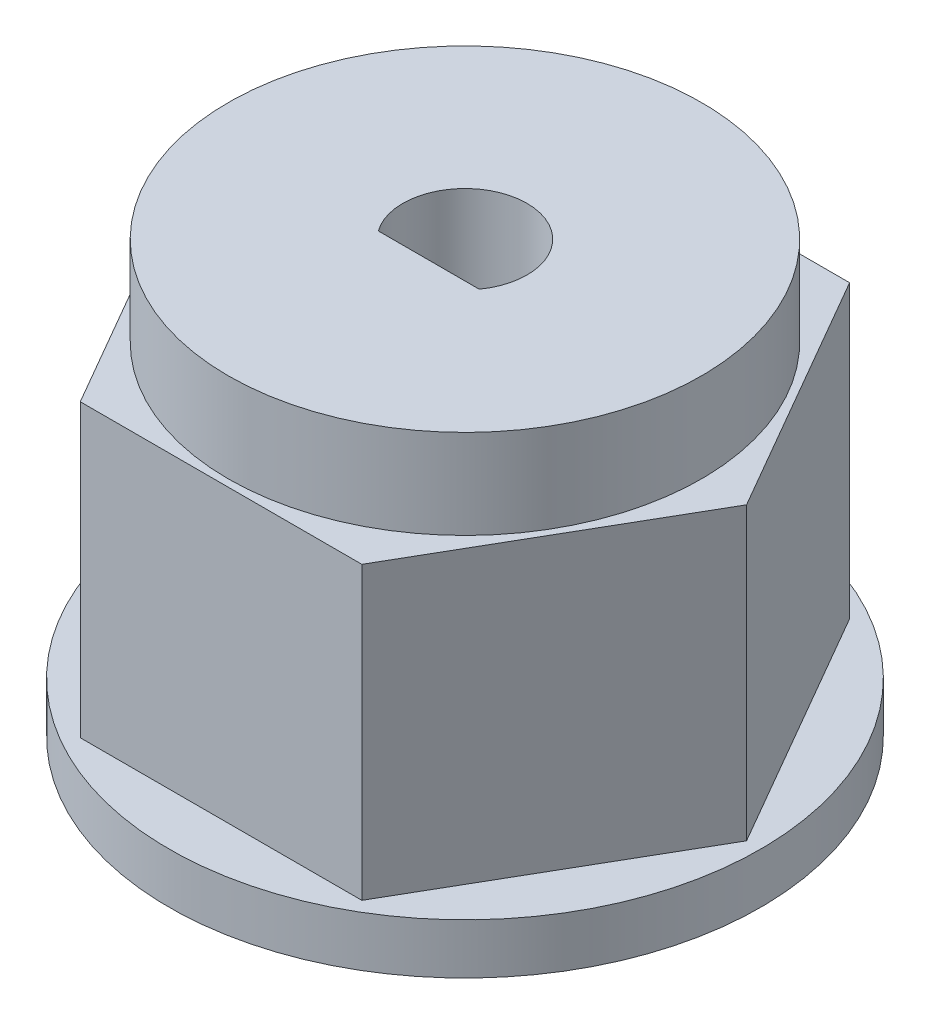
SolidWorks part; units mm, degrees
ref_plane "Front Plane" through (0, 0, 0) normal (0, 0, 1) x (1, 0, 0)
ref_plane "Top Plane" through (0, 0, 0) normal (0, 1, 0) x (1, 0, 0)
ref_plane "Right Plane" through (0, 0, 0) normal (1, 0, 0) x (0, 0, -1)
sketch "Sketch1" plane through (0, 0, 0) normal (0, 1, 0) x (1, 0, 0)
  line L1 (7.2573, 0) -> (3.6286, 6.285)
  line L2 (3.6286, 6.285) -> (-3.6286, 6.285)
  line L3 (-3.6286, 6.285) -> (-7.2573, 0)
  line L4 (-7.2573, 0) -> (-3.6286, -6.285)
  line L5 (-3.6286, -6.285) -> (3.6286, -6.285)
  line L6 (3.6286, -6.285) -> (7.2573, 0)
  circle A0 centre (0, 0) radius 6.285 construction
  dimension "D1" = 12.57
extrude "Boss-Extrude1" add sketch "Sketch1" along normal blind 7.5
sketch "Sketch2" plane through (0, 7.5, 0) normal (0, 1, 0) x (1, 0, 0)
  circle A0 centre (0, 0) radius 6.1
  dimension "D1" = 12.2
extrude "Boss-Extrude2" add sketch "Sketch2" along normal blind 2.3
sketch "Sketch3" plane through (0, 0, 0) normal (0, -1, 0) x (1, 0, 0)
  circle A0 centre (0, 0) radius 7.625
  dimension "D1" = 15.25
extrude "Boss-Extrude3" add sketch "Sketch3" along normal blind 1.3
sketch "Sketch4" plane through (0, 9.8, 0) normal (0, 1, 0) x (1, 0, 0)
  line L0 (-1.3, -0.9327) -> (1.3, -0.9327)
  arc A0 (1.3, -0.9327) -> (-1.3, -0.9327) centre (0, 0) ccw
  dimension "D1" = 3.2
  dimension "D2" = 2.6
extrude "Cut-Extrude1" cut sketch "Sketch4" against normal through all
